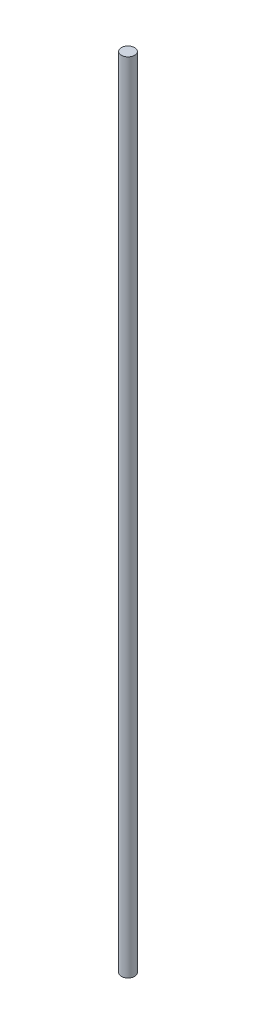
SolidWorks part; units mm, degrees
ref_plane "Front Plane" through (0, 0, 0) normal (0, 0, 1) x (1, 0, 0)
ref_plane "Top Plane" through (0, 0, 0) normal (0, 1, 0) x (1, 0, 0)
ref_plane "Right Plane" through (0, 0, 0) normal (1, 0, 0) x (0, 0, -1)
sketch "Sketch1" plane through (0, 0, 0) normal (0, 1, 0) x (1, 0, 0)
  circle A0 centre (0, 0) radius 10
  dimension "D1" = 20
extrude "Boss-Extrude1" add sketch "Sketch1" along normal blind 1200
